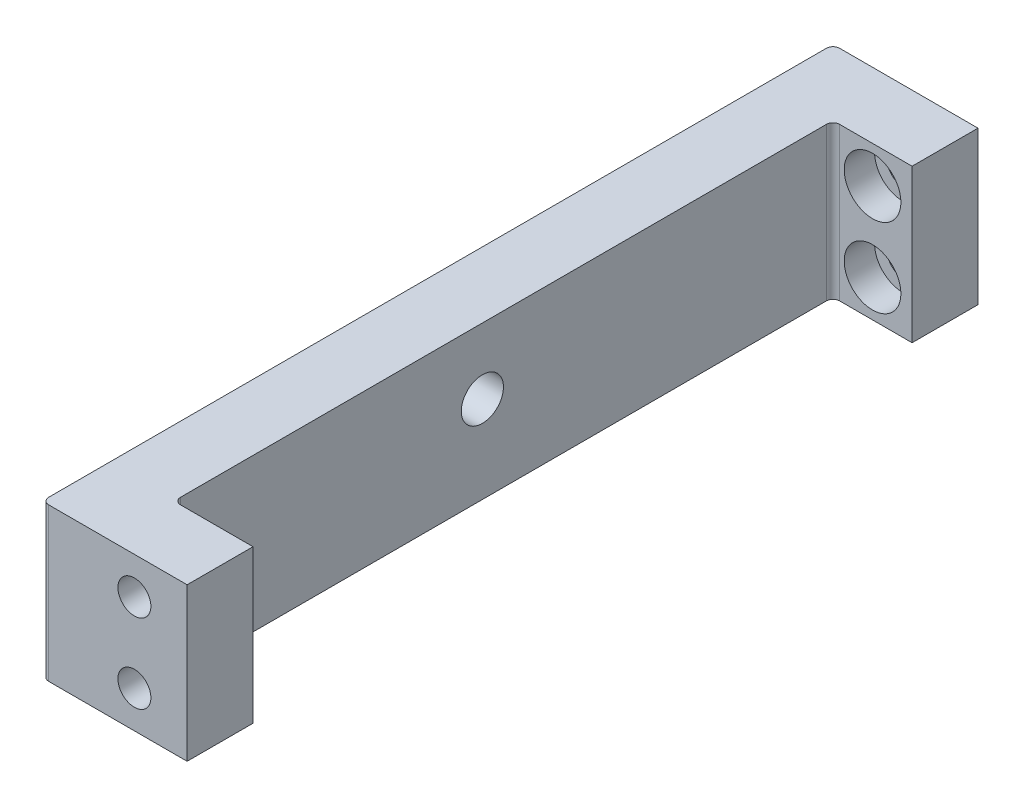
SolidWorks part; units mm, degrees
ref_plane "前视基准面" through (0, 0, 0) normal (0, 0, 1) x (1, 0, 0)
ref_plane "上视基准面" through (0, 0, 0) normal (0, 1, 0) x (1, 0, 0)
ref_plane "右视基准面" through (0, 0, 0) normal (1, 0, 0) x (0, 0, -1)
sketch "草图1" plane through (0, 0, 0) normal (0, 0, 1) x (1, 0, 0)
  line L1 (2.5, -5.8) -> (-2.5, -5.8)
  line L2 (2.5, -5.8) -> (2.5, 5.8)
  line L3 (2.5, 5.8) -> (-2.5, 5.8)
  line L4 (-2.5, -5.8) -> (-2.5, 5.8)
  line L5 (2.5, -5.8) -> (-2.5, 5.8) construction
  line L6 (2.5, 5.8) -> (-2.5, -5.8) construction
  point P0 (0, 0)
  dimension "D1" = 5
  dimension "D2" = 11.6
extrude "凸台-拉伸1" add sketch "草图1" along normal mid plane 60
sketch "草图2" plane through (2.5, 0, 0) normal (1, 0, 0) x (0, 0, -1)
  line L0 (-30, -5.8) -> (-30, 5.8)
  line L1 (-30, 5.8) -> (-25, 5.8)
  line L2 (-30, 5.8) -> (30, 5.8) construction
  line L3 (-25, 5.8) -> (-25, -5.8)
  line L4 (-30, -5.8) -> (30, -5.8) construction
  line L5 (-25, -5.8) -> (-30, -5.8)
  dimension "D1" = 5
extrude "凸台-拉伸2" add sketch "草图2" along normal blind 6
mirror "镜向1" about plane through (0, 0, 0) normal (0, 0, 1) of "凸台-拉伸2"
hole_wizard "M3 螺纹孔1" positions "草图3" profile "草图4" tap size "M3" standard "GB"
sketch "草图3" plane through (0, 0, 30) normal (0, 0, 1) x (1, 0, 0)
  line L0 (8.5, 5.8) -> (8.5, -5.8) construction
  point P0 (4.5, -3)
  point P2 (4.5, 3)
  dimension "D1" = 6
  dimension "D2" = 3
  dimension "D3" = 4
sketch "草图4" plane through (4.5, -3, 30) normal (1, 0, 0) x (0, -1, 0)
  line L0 (0, 0) -> (0, 8.2511)
  line L1 (0, 8.2511) -> (1.25, 7.5)
  line L2 (1.25, 7.5) -> (1.25, 0)
  line L5 (1.25, 0) -> (0, 0)
  line L10 (0, 8.2511) -> (-1.25, 7.5) construction
  line L11 (0, -6.35) -> (0, 107.95) construction
  dimension "螺纹孔钻头直径" = 2.5
  dimension "螺纹孔钻头深度" = 7.5
  dimension "导头角度" = 118
cosmetic thread "孔螺蚊线1" parameters "D1"=5, "D2"=3
cosmetic thread "孔螺蚊线2" parameters "D1"=5, "D2"=3
hole_wizard "打孔尺寸(%根据)内六角圆柱头螺钉的类型1" positions "草图7" profile "草图6" counterbore size "M2" standard "GB"
sketch "草图7" plane through (0, 0, -25) normal (0, 0, 1) x (1, 0, 0)
  line L0 (8.5, -5.8) -> (8.5, 5.8) construction
  point P0 (5.5, -3)
  point P2 (5.5, 3)
  dimension "D1" = 6
  dimension "D2" = 3
  dimension "D3" = 3
sketch "草图6" plane through (5.5, -3, -25) normal (1, 0, 0) x (0, -1, 0)
  line L0 (0, 0) -> (0, 8.221)
  line L1 (0, 8.221) -> (1.2, 7.5)
  line L2 (1.2, 7.5) -> (1.2, 2.3)
  line L3 (1.2, 2.3) -> (2.15, 2.3)
  line L4 (2.15, 2.3) -> (2.15, 0)
  line L5 (2.15, 0) -> (0, 0)
  line L10 (0, 8.221) -> (-1.2, 7.5) construction
  line L11 (0, -6.35) -> (0, 107.95) construction
  dimension "孔直径" = 2.4
  dimension "孔深度" = 7.5
  dimension "柱形沉头孔直径" = 4.3
  dimension "柱形沉头孔深度" = 2.3
  dimension "导头角度" = 118
fillet "圆角1" radius 0.5 4 edges at (-2.5, 0, -30) (2.5, 0, -25) (2.5, 0, 25) (-2.5, 0, 30)
hole_wizard "Ø3.2 (3.2) 直径孔1" positions "草图8" profile "草图9" hole size "Ø3.2" standard "GB"
sketch "草图8" plane through (-2.5, 0, 0) normal (-1, 0, 0) x (0, 0, 1)
  point P0 (1.6, 0.8)
sketch "草图9" plane through (-2.5, 0.8, 1.6) normal (0, 1, 0) x (0, 0, 1)
  line L0 (0, 0) -> (0, 6.1614)
  line L1 (0, 6.1614) -> (1.6, 5.2)
  line L2 (1.6, 5.2) -> (1.6, 0)
  line L5 (1.6, 0) -> (0, 0)
  line L10 (0, 6.1614) -> (-1.6, 5.2) construction
  line L11 (0, -6.35) -> (0, 107.95) construction
  dimension "孔直径" = 3.2
  dimension "孔深度" = 5.2
  dimension "导头角度" = 118
hole_wizard "M2 螺纹孔1" positions "草图10" profile "草图12" tap size "M2" standard "GB"
sketch "草图10" plane through (0, -5.8, 0) normal (0, -1, 0) x (-1, 0, 0)
  point P0 (-0.325, 9)
sketch "草图12" plane through (0.325, -5.8, -9) normal (1, 0, 0) x (0, 0, -1)
  line L0 (0, 0) -> (0, 5.6807)
  line L1 (0, 5.6807) -> (0.8, 5.2)
  line L2 (0.8, 5.2) -> (0.8, 0)
  line L5 (0.8, 0) -> (0, 0)
  line L10 (0, 5.6807) -> (-0.8, 5.2) construction
  line L11 (0, -6.35) -> (0, 107.95) construction
  dimension "螺纹孔钻头直径" = 1.6
  dimension "螺纹孔钻头深度" = 5.2
  dimension "导头角度" = 118
cosmetic thread "孔螺蚊线3" parameters "D1"=4, "D2"=2
